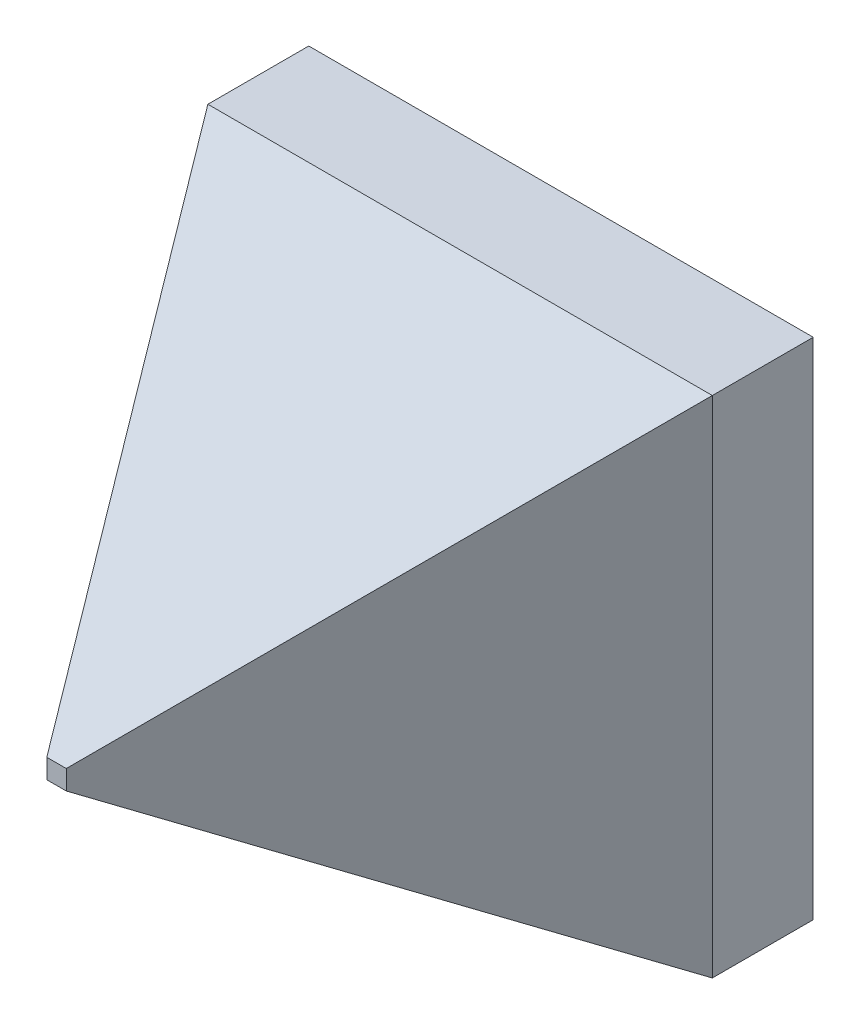
SolidWorks part; units mm, degrees
material "Plastique personnalisé"
ref_plane "Plan de face" through (0, 0, 0) normal (0, 0, 1) x (1, 0, 0)
ref_plane "Plan de dessus" through (0, 0, 0) normal (0, 1, 0) x (1, 0, 0)
ref_plane "Plan de droite" through (0, 0, 0) normal (1, 0, 0) x (0, 0, -1)
sketch "cellule" plane through (0, 0, 0) normal (0, 0, 1) x (1, 0, 0)
  line L1 (-25, -25) -> (25, -25)
  line L2 (-25, -25) -> (-25, 25)
  line L3 (-25, 25) -> (25, 25)
  line L4 (25, -25) -> (25, 25)
  line L5 (-25, -25) -> (25, 25) construction
  line L6 (-25, 25) -> (25, -25) construction
  point P0 (0, 0)
  dimension "D1" = 50
  dimension "D2" = 50
extrude "Boss.-Extru.1" add sketch "cellule" against normal blind 10
sketch "Esquisse2" plane through (0, 0, 0) normal (0, 0, 1) x (1, 0, 0)
  line L1 (-25, -25) -> (25, -25)
  line L2 (-25, -25) -> (-25, 25)
  line L3 (-25, 25) -> (25, 25)
  line L4 (25, -25) -> (25, 25)
  line L5 (-25, -25) -> (25, 25) construction
  line L6 (-25, 25) -> (25, -25) construction
  point P0 (0, 0)
extrude "Boss.-Extru.2" add sketch "Esquisse2" along normal blind 40 draft 31
